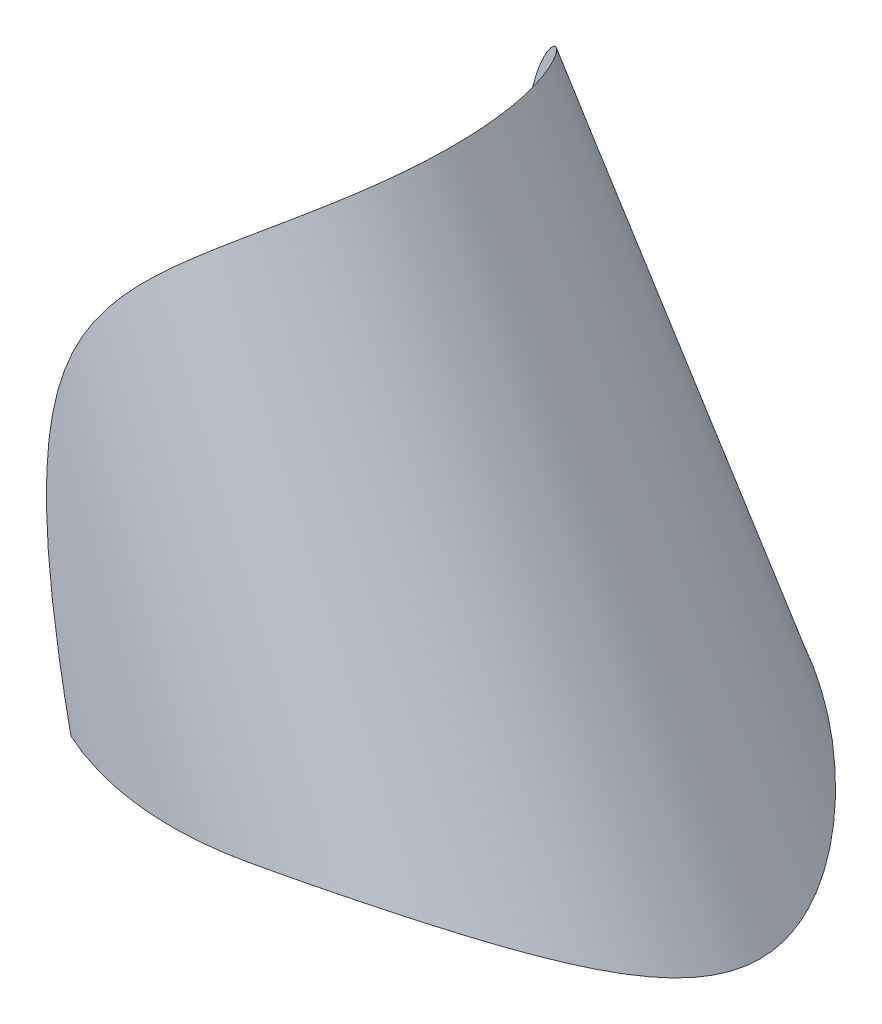
SolidWorks part; units mm, degrees
ref_plane "Plan de face" through (0, 0, 0) normal (0, 0, 1) x (1, 0, 0)
ref_plane "Plan de dessus" through (0, 0, 0) normal (0, 1, 0) x (1, 0, 0)
ref_plane "Plan de droite" through (0, 0, 0) normal (1, 0, 0) x (0, 0, -1)
sketch "Esquisse6" plane through (0, 0, 0) normal (0, 0, 1) x (1, 0, 0)
  line L0 (30.2546, 29.0234) -> (49.8378, -5.9766)
  line L1 (30.2546, 29.0234) -> (32, 30)
  line L2 (32, 30) -> (51.5831, -5)
  line L3 (51.5831, -5) -> (49.8378, -5.9766)
  line L7 (16, 30) -> (43.0834, -28.0805) construction
  line L9 (16, 30) -> (16, -28.0805) construction
  dimension "D1" = 2
  dimension "D2" = 30
  dimension "D3" = 5
  dimension "D4" = 16
  dimension "D5" = 25
  dimension "D6" = 16
  dimension "D7" = 35.5831
revolve "Révolution3" add sketch "Esquisse6" angle 360 about L7
sketch "Esquisse7" plane through (0, 0, 0) normal (0, 1, 0) x (1, 0, 0)
  circle A0 centre (16, 0) radius 16
  dimension "D1" = 32
extrude "Enlèv. mat.-Extru.4" cut sketch "Esquisse7" against normal through all and the other way through all
sketch "Esquisse8" plane through (0, 0, 0) normal (0, 0, 1) x (1, 0, 0)
  line L1 (0, 0) -> (35, 0)
  line L2 (0, 0) -> (0, -30)
  line L3 (0, -30) -> (65, -30)
  arc A0 (65, -30) -> (35, 0) centre (35, -30) ccw
  point P7 (65, 0)
  dimension "D2" = 30
  dimension "D1" = 65
extrude "Enlèv. mat.-Extru.5" cut sketch "Esquisse8" against normal through all and the other way through all
